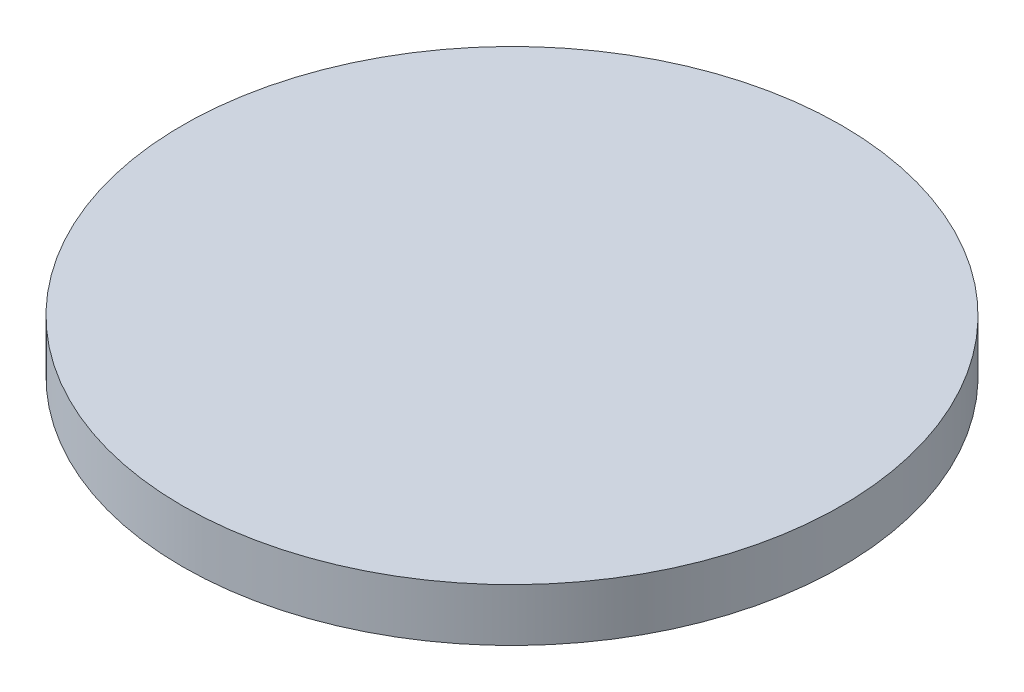
SolidWorks part; units mm, degrees
ref_plane "Front Plane" through (0, 0, 0) normal (0, 0, 1) x (1, 0, 0)
ref_plane "Top Plane" through (0, 0, 0) normal (0, 1, 0) x (1, 0, 0)
ref_plane "Right Plane" through (0, 0, 0) normal (1, 0, 0) x (0, 0, -1)
sketch "Sketch1" plane through (0, 0, 0) normal (0, 1, 0) x (1, 0, 0)
  circle A0 centre (0, 0) radius 19.8437
  dimension "D1" = 39.6875
extrude "Boss-Extrude1" add sketch "Sketch1" along normal blind 3.175
